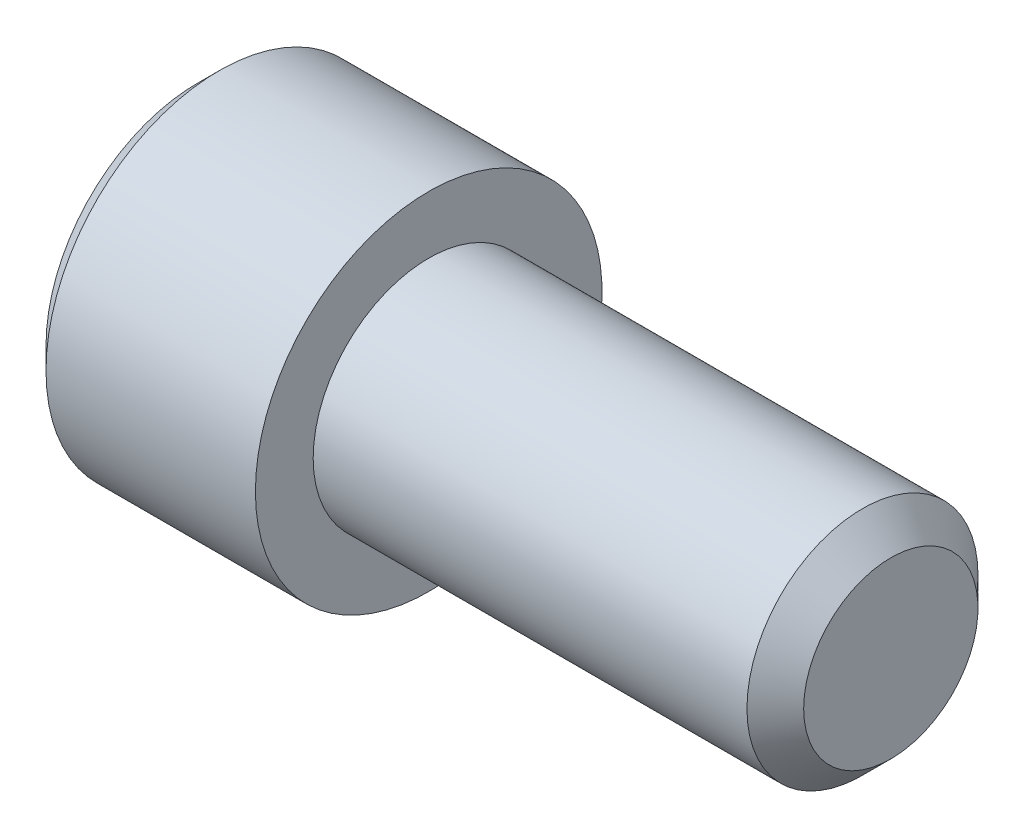
SolidWorks part; units mm, degrees
material "AISI 304"
ref_plane "正面" through (0, 0, 0) normal (0, 0, 1) x (1, 0, 0)
ref_plane "平面" through (0, 0, 0) normal (0, 1, 0) x (1, 0, 0)
ref_plane "右側面" through (0, 0, 0) normal (1, 0, 0) x (0, 0, -1)
ref_plane "Plane1" through (0, 0, 0) normal (0, 0, 1) x (1, 0, 0)
sketch "Sketch1" plane through (0, 0, 0) normal (0, 0, 1) x (1, 0, 0)
  line L0 (-2, 0) -> (-2, 1.3125)
  line L1 (-2, 1.3125) -> (-1.8125, 1.5)
  line L2 (-1.8125, 1.5) -> (0, 1.5)
  line L3 (0, 1.5) -> (0, 1)
  line L4 (0, 1) -> (3.7545, 1)
  line L5 (3.7545, 1) -> (4, 0.7545)
  line L6 (4, 0.7545) -> (4, 0)
  line L7 (4, 0) -> (-2, 0)
  line L8 (4, 0) -> (-2, 0) construction
revolve "Revolve1" add sketch "Sketch1" angle 360 about L8
cosmetic thread "Cosmetic Thread1" parameters "D1"=3.5, "D2"=1.509
ref_plane "Plane2" through (0, 0, 0) normal (0, 0, 1) x (1, 0, 0)
sketch "Sketch2" plane through (0, 0, 0) normal (0, 0, 1) x (1, 0, 0)
  line L0 (-2, 0) -> (-2, 0.9)
  line L1 (-2, 0.9) -> (-1.85, 0.75)
  line L2 (-1.85, 0.75) -> (-1, 0.75)
  line L3 (-1, 0.75) -> (-0.6, 0)
  line L4 (-0.6, 0) -> (-2, 0)
  line L5 (-0.6, 0) -> (-2, 0) construction
revolve "Cut-Revolve1" cut sketch "Sketch2" angle 360 about L5
ref_plane "Plane3" through (-2, 0, 0) normal (1, 0, 0) x (0, 0, -1)
sketch "Sketch3" plane through (-2, 0, 0) normal (1, 0, 0) x (0, 0, -1)
  line L0 (-0.75, -0.433) -> (0, -0.866)
  line L1 (0, -0.866) -> (0.75, -0.433)
  line L2 (0.75, -0.433) -> (0.75, 0.433)
  line L3 (0.75, 0.433) -> (0, 0.866)
  line L4 (0, 0.866) -> (-0.75, 0.433)
  line L5 (-0.75, 0.433) -> (-0.75, -0.433)
extrude "Cut-Extrude1" cut sketch "Sketch3" along normal blind 1
